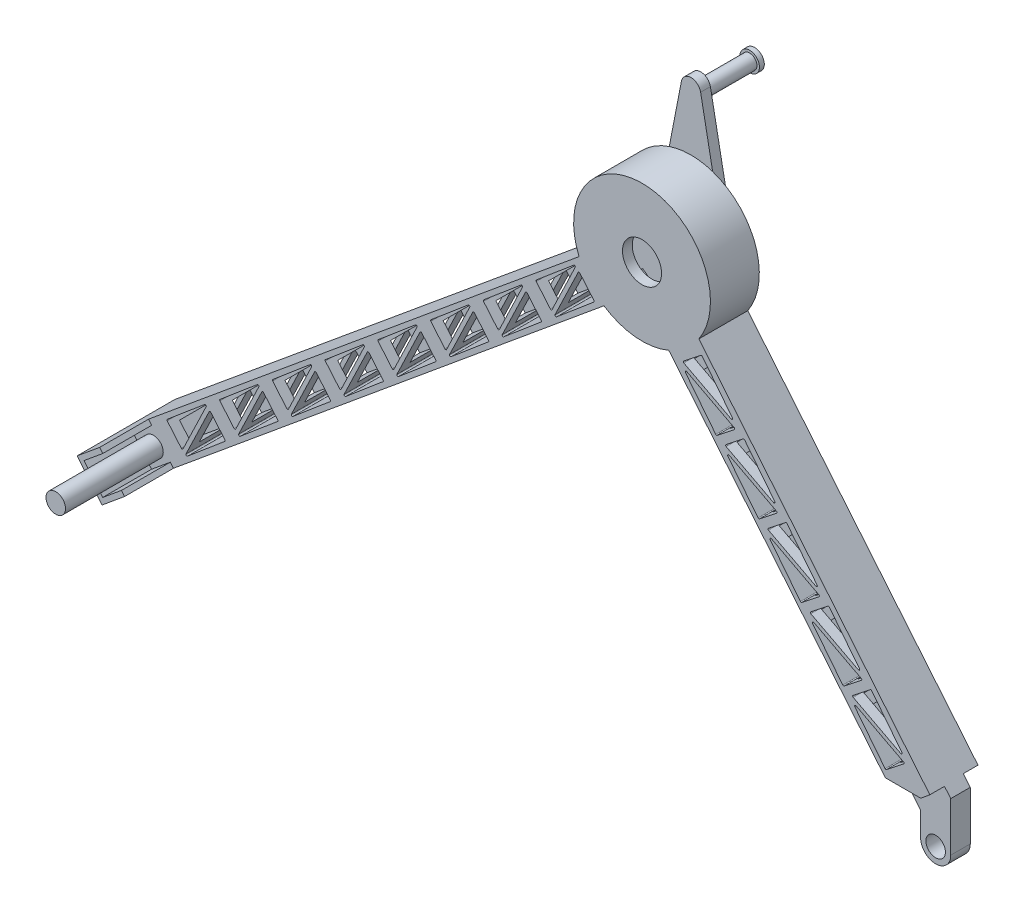
SolidWorks part; units mm, degrees
ref_plane "Front Plane" through (0, 0, 0) normal (0, 0, 1) x (1, 0, 0)
ref_plane "Top Plane" through (0, 0, 0) normal (0, 1, 0) x (1, 0, 0)
ref_plane "Right Plane" through (0, 0, 0) normal (1, 0, 0) x (0, 0, -1)
sketch "Sketch1" plane through (0, 0, 0) normal (0, 0, 1) x (1, 0, 0)
  line L0 (-491.963, 0) -> (712.4353, 0) construction
  line L3 (-479.2178, -15.413) -> (-19.4352, 364.7883)
  line L4 (46.852, 358.5081) -> (289.5642, 64.9929)
  line L5 (-504.7082, 15.413) -> (-44.9257, 395.6142)
  line L6 (77.6779, 383.9986) -> (320.3902, 90.4834)
  line L7 (-504.7082, 15.413) -> (-479.2178, -15.413)
  line L8 (289.5642, 64.9929) -> (320.3902, 90.4834)
  arc A0 (-19.4352, 364.7883) -> (46.852, 358.5081) centre (19.5162, 422.95) ccw
  arc A1 (77.6779, 383.9986) -> (-44.9257, 395.6142) centre (19.5162, 422.95) ccw
  dimension "D4" = 140
  dimension "D1" = 663.7
  dimension "D3" = 422.95
extrude "Boss-Extrude1" add sketch "Sketch1" along normal blind 50
shell "Shell1" thickness 10
sketch "Sketch2" plane through (0, 0, 0) normal (0, 0, 1) x (1, 0, 0)
  line L0 (289.5642, 64.9929) -> (289.5642, 40.3364)
  line L1 (46.852, 358.5081) -> (289.5642, 64.9929) construction
  line L2 (289.5642, 64.9929) -> (320.3902, 90.4834) construction
  line L3 (289.5642, 64.9929) -> (320.3902, 90.4834)
  line L4 (320.3902, 90.4834) -> (320.3902, 40.3364)
  arc A0 (289.5642, 40.3364) -> (320.3902, 40.3364) centre (304.9772, 40.3364) ccw
extrude "Boss-Extrude2" add sketch "Sketch2" along normal blind 50
sketch "Sketch3" plane through (0, 0, 50) normal (0, 0, 1) x (1, 0, 0)
  circle A0 centre (304.9772, 40.3364) radius 10
  dimension "D1" = 20
extrude "Cut-Extrude1" cut sketch "Sketch3" against normal blind 50
sketch "Sketch4" plane through (320.3902, 0, 0) normal (1, 0, 0) x (0, 0, -1)
  line L0 (-50, 24.9234) -> (0, 24.9234) construction
  line L1 (-50, 90.4834) -> (-35, 90.4834)
  line L2 (-50, 90.4834) -> (-50, 24.9234)
  line L3 (-50, 24.9234) -> (-35, 24.9234)
  line L4 (-35, 90.4834) -> (-35, 24.9234)
  line L6 (0, 90.4834) -> (-15, 90.4834)
  line L7 (0, 90.4834) -> (0, 24.9234)
  line L8 (0, 24.9234) -> (-15, 24.9234)
  line L9 (-15, 90.4834) -> (-15, 24.9234)
  dimension "D1" = 20
extrude "Cut-Extrude2" cut sketch "Sketch4" against normal blind 50
sketch "Sketch6" plane through (270.3902, 0, 0) normal (1, 0, 0) x (0, 0, -1)
  line L0 (-50, 88.1804) -> (-35, 88.1804) construction
  line L1 (-50, 90.4834) -> (-35.0332, 90.4834)
  line L2 (-50, 90.4834) -> (-50, 88.1804)
  line L3 (-50, 88.1804) -> (-35.0332, 88.1804)
  line L4 (-35.0332, 90.4834) -> (-35.0332, 88.1804)
  line L5 (0, -15.413) -> (0, 364.7883) construction
  line L6 (-15, 90.4834) -> (0, 90.4834)
  line L7 (-15, 90.4834) -> (-15, 88.1804)
  line L8 (-15, 88.1804) -> (0, 88.1804)
  line L9 (0, 90.4834) -> (0, 88.1804)
  line L10 (0, 88.1804) -> (-15, 88.1804) construction
extrude "Cut-Extrude3" cut sketch "Sketch6" against normal blind 50
sketch "Sketch7" plane through (0, 0, 50) normal (0, 0, 1) x (1, 0, 0)
  line L0 (304.698, 90.4834) -> (314.0176, 98.1898)
  line L1 (320.3902, 90.4834) -> (77.6779, 383.9986) construction
  line L2 (314.0176, 98.1898) -> (320.3902, 90.4834)
  line L3 (320.3902, 90.4834) -> (304.698, 90.4834)
  line L4 (304.698, 90.4834) -> (320.3902, 90.4834) construction
extrude "Cut-Extrude4" cut sketch "Sketch7" against normal up to surface (15 mm away) up to face at (293.083, 73.2709, 35)
sketch "Sketch8" plane through (0, 0, 0) normal (0, 0, -1) x (-1, 0, 0)
  line L0 (-304.698, 90.4834) -> (-313.2874, 99.0728)
  line L1 (-320.3902, 90.4834) -> (-77.6779, 383.9986) construction
  line L2 (-313.2874, 99.0728) -> (-320.3902, 90.4834)
  line L3 (-320.3902, 90.4834) -> (-304.698, 90.4834)
extrude "Cut-Extrude5" cut sketch "Sketch8" against normal up to surface (15 mm away) up to face at (295.6816, 71.4073, 15)
sketch "Sketch9" plane through (0, 0, 0) normal (0, 0, 1) x (1, 0, 0)
  line L0 (-504.7082, 15.413) -> (-479.2178, -15.413)
  line L1 (-479.2178, -15.413) -> (-483.071, -18.5993)
  line L2 (-483.071, -18.5993) -> (-508.5615, 12.2267)
  line L3 (-508.5615, 12.2267) -> (-504.7082, 15.413)
  dimension "D1" = 5
extrude "Boss-Extrude3" add sketch "Sketch9" along normal blind 100
sketch "Sketch10" plane through (0, 0, 50) normal (0, 0, 1) x (1, 0, 0)
  line L0 (-479.2178, -15.413) -> (-459.9516, 0.5186)
  line L1 (-479.2178, -15.413) -> (-19.4352, 364.7883) construction
  line L2 (-459.9516, 0.5186) -> (-463.1379, 4.3718)
  line L3 (-463.1379, 4.3718) -> (-482.4041, -11.5597)
  line L4 (-504.7082, 15.413) -> (-479.2178, -15.413) construction
  line L5 (-482.4041, -11.5597) -> (-479.2178, -15.413)
  line L6 (-504.7082, 15.413) -> (-485.442, 31.3445)
  line L7 (-44.9257, 395.6142) -> (-504.7082, 15.413) construction
  line L8 (-485.442, 31.3445) -> (-482.2557, 27.4912)
  line L9 (-482.2557, 27.4912) -> (-501.5219, 11.5597)
  line L10 (-501.5219, 11.5597) -> (-504.7082, 15.413)
  dimension "D1" = 5
  dimension "D2" = 25
extrude "Boss-Extrude4" add sketch "Sketch10" along normal up to surface (50 mm away) up to face at (-493.8896, -1.5932, 100)
sketch "Sketch11" plane through (0, 0, 50) normal (0, 0, 1) x (1, 0, 0)
  line L0 (-466.2504, 40.8221) -> (-428.047, 73.0788)
  line L1 (-426.5003, 71.8821) -> (-450.2175, 22.4684)
  line L2 (-451.8831, 22.256) -> (-466.3694, 39.4129)
  line L3 (-445.6127, 18.399) -> (-407.4092, 50.6557)
  line L4 (-407.2903, 52.0649) -> (-421.7766, 69.2218)
  line L5 (-423.4422, 69.0094) -> (-447.1594, 19.5958)
  line L9 (-44.9257, 395.6142) -> (-485.442, 31.3445) construction
  line L10 (-44.9257, 395.6142) -> (-485.442, 31.3445)
  line L11 (-470.773, 43.4745) -> (-429.0952, 77.9385)
  line L14 (-397.9377, 66.8642) -> (-412.424, 84.0212)
  line L15 (-412.3051, 85.4304) -> (-374.1016, 117.6871)
  line L16 (-372.5549, 116.4903) -> (-396.2721, 67.0767)
  line L17 (-369.4968, 113.6177) -> (-393.214, 64.204)
  line L18 (-391.6673, 63.0072) -> (-353.4639, 95.2639)
  line L19 (-353.3449, 96.6731) -> (-367.8312, 113.8301)
  line L20 (-343.9923, 111.4725) -> (-358.4786, 128.6294)
  line L21 (-358.3597, 130.0386) -> (-320.1562, 162.2954)
  line L22 (-318.6095, 161.0986) -> (-342.3267, 111.6849)
  line L23 (-315.5514, 158.2259) -> (-339.2686, 108.8123)
  line L24 (-337.722, 107.6155) -> (-299.5185, 139.8722)
  line L25 (-299.3996, 141.2814) -> (-313.8858, 158.4383)
  line L26 (-290.047, 156.0808) -> (-304.5332, 173.2377)
  line L27 (-304.4143, 174.6469) -> (-266.2108, 206.9036)
  line L28 (-264.6642, 205.7068) -> (-288.3813, 156.2932)
  line L29 (-261.6061, 202.8342) -> (-285.3233, 153.4205)
  line L30 (-283.7766, 152.2237) -> (-245.5731, 184.4805)
  line L31 (-245.4542, 185.8897) -> (-259.9405, 203.0466)
  line L32 (-236.1016, 200.689) -> (-250.5879, 217.846)
  line L33 (-250.4689, 219.2552) -> (-212.2655, 251.5119)
  line L34 (-210.7188, 250.3151) -> (-234.436, 200.9014)
  line L35 (-207.6607, 247.4424) -> (-231.3779, 198.0288)
  line L36 (-229.8312, 196.832) -> (-191.6277, 229.0887)
  line L37 (-191.5088, 230.4979) -> (-205.9951, 247.6549)
  line L38 (-182.1562, 245.2973) -> (-196.6425, 262.4542)
  line L39 (-196.5236, 263.8634) -> (-158.3201, 296.1201)
  line L40 (-156.7734, 294.9233) -> (-180.4906, 245.5097)
  line L41 (-153.7153, 292.0507) -> (-177.4325, 242.637)
  line L42 (-175.8858, 241.4403) -> (-137.6824, 273.697)
  line L43 (-137.5634, 275.1062) -> (-152.0497, 292.2631)
  line L44 (-128.2108, 289.9055) -> (-142.6971, 307.0625)
  line L45 (-142.5782, 308.4717) -> (-104.3747, 340.7284)
  line L46 (-102.828, 339.5316) -> (-126.5452, 290.118)
  line L47 (-99.7699, 336.6589) -> (-123.4871, 287.2453)
  line L48 (-121.9405, 286.0485) -> (-83.737, 318.3052)
  line L49 (-83.6181, 319.7144) -> (-98.1043, 336.8714)
  line L50 (-74.2655, 334.5138) -> (-88.7517, 351.6707)
  line L51 (-88.6328, 353.0799) -> (-50.4293, 385.3366)
  line L52 (-48.8827, 384.1399) -> (-72.5999, 334.7262)
  line L53 (-45.8246, 381.2672) -> (-69.5418, 331.8536)
  line L54 (-67.9951, 330.6568) -> (-29.7916, 362.9135)
  line L55 (-29.6727, 364.3227) -> (-44.159, 381.4796)
  arc A0 (-445.6127, 18.399) -> (-447.1594, 19.5958) centre (-446.2578, 19.163) cw
  arc A1 (-407.4092, 50.6557) -> (-407.2903, 52.0649) centre (-408.0544, 51.4197) ccw
  arc A2 (-421.7766, 69.2218) -> (-423.4422, 69.0094) centre (-422.5407, 68.5767) ccw
  arc A3 (-450.2175, 22.4684) -> (-451.8831, 22.256) centre (-451.119, 22.9011) cw
  arc A4 (-466.3694, 39.4129) -> (-466.2504, 40.8221) centre (-465.6053, 40.0581) cw
  arc A5 (-426.5003, 71.8821) -> (-428.047, 73.0788) centre (-427.4018, 72.3148) ccw
  arc A6 (-412.424, 84.0212) -> (-412.3051, 85.4304) centre (-411.6599, 84.6663) cw
  arc A7 (-396.2721, 67.0767) -> (-397.9377, 66.8642) centre (-397.1736, 67.5094) cw
  arc A8 (-372.5549, 116.4903) -> (-374.1016, 117.6871) centre (-373.4564, 116.923) ccw
  arc A9 (-367.8312, 113.8301) -> (-369.4968, 113.6177) centre (-368.5953, 113.1849) ccw
  arc A10 (-391.6673, 63.0072) -> (-393.214, 64.204) centre (-392.3125, 63.7713) cw
  arc A11 (-353.4639, 95.2639) -> (-353.3449, 96.6731) centre (-354.109, 96.028) ccw
  arc A12 (-358.4786, 128.6294) -> (-358.3597, 130.0386) centre (-357.7145, 129.2746) cw
  arc A13 (-342.3267, 111.6849) -> (-343.9923, 111.4725) centre (-343.2283, 112.1176) cw
  arc A14 (-318.6095, 161.0986) -> (-320.1562, 162.2954) centre (-319.5111, 161.5313) ccw
  arc A15 (-313.8858, 158.4383) -> (-315.5514, 158.2259) centre (-314.6499, 157.7932) ccw
  arc A16 (-337.722, 107.6155) -> (-339.2686, 108.8123) centre (-338.3671, 108.3796) cw
  arc A17 (-299.5185, 139.8722) -> (-299.3996, 141.2814) centre (-300.1636, 140.6363) ccw
  arc A18 (-304.5332, 173.2377) -> (-304.4143, 174.6469) centre (-303.7692, 173.8828) cw
  arc A19 (-288.3813, 156.2932) -> (-290.047, 156.0808) centre (-289.2829, 156.7259) cw
  arc A20 (-264.6642, 205.7068) -> (-266.2108, 206.9036) centre (-265.5657, 206.1395) ccw
  arc A21 (-259.9405, 203.0466) -> (-261.6061, 202.8342) centre (-260.7045, 202.4015) ccw
  arc A22 (-283.7766, 152.2237) -> (-285.3233, 153.4205) centre (-284.4217, 152.9878) cw
  arc A23 (-245.5731, 184.4805) -> (-245.4542, 185.8897) centre (-246.2183, 185.2445) ccw
  arc A24 (-250.5879, 217.846) -> (-250.4689, 219.2552) centre (-249.8238, 218.4911) cw
  arc A25 (-234.436, 200.9014) -> (-236.1016, 200.689) centre (-235.3375, 201.3341) cw
  arc A26 (-210.7188, 250.3151) -> (-212.2655, 251.5119) centre (-211.6203, 250.7478) ccw
  arc A27 (-205.9951, 247.6549) -> (-207.6607, 247.4424) centre (-206.7592, 247.0097) ccw
  arc A28 (-229.8312, 196.832) -> (-231.3779, 198.0288) centre (-230.4763, 197.5961) cw
  arc A29 (-191.6277, 229.0887) -> (-191.5088, 230.4979) centre (-192.2729, 229.8528) ccw
  arc A30 (-196.6425, 262.4542) -> (-196.5236, 263.8634) centre (-195.8784, 263.0993) cw
  arc A31 (-180.4906, 245.5097) -> (-182.1562, 245.2973) centre (-181.3921, 245.9424) cw
  arc A32 (-156.7734, 294.9233) -> (-158.3201, 296.1201) centre (-157.6749, 295.3561) ccw
  arc A33 (-152.0497, 292.2631) -> (-153.7153, 292.0507) centre (-152.8138, 291.618) ccw
  arc A34 (-175.8858, 241.4403) -> (-177.4325, 242.637) centre (-176.531, 242.2043) cw
  arc A35 (-137.6824, 273.697) -> (-137.5634, 275.1062) centre (-138.3275, 274.461) ccw
  arc A36 (-142.6971, 307.0625) -> (-142.5782, 308.4717) centre (-141.933, 307.7076) cw
  arc A37 (-126.5452, 290.118) -> (-128.2108, 289.9055) centre (-127.4468, 290.5507) cw
  arc A38 (-102.828, 339.5316) -> (-104.3747, 340.7284) centre (-103.7296, 339.9643) ccw
  arc A39 (-98.1043, 336.8714) -> (-99.7699, 336.6589) centre (-98.8684, 336.2262) ccw
  arc A40 (-121.9405, 286.0485) -> (-123.4871, 287.2453) centre (-122.5856, 286.8126) cw
  arc A41 (-83.737, 318.3052) -> (-83.6181, 319.7144) centre (-84.3821, 319.0693) ccw
  arc A42 (-88.7517, 351.6707) -> (-88.6328, 353.0799) centre (-87.9877, 352.3159) cw
  arc A43 (-72.5999, 334.7262) -> (-74.2655, 334.5138) centre (-73.5014, 335.1589) cw
  arc A44 (-48.8827, 384.1399) -> (-50.4293, 385.3366) centre (-49.7842, 384.5726) ccw
  arc A45 (-44.159, 381.4796) -> (-45.8246, 381.2672) centre (-44.923, 380.8345) ccw
  arc A46 (-67.9951, 330.6568) -> (-69.5418, 331.8536) centre (-68.6402, 331.4208) cw
  arc A47 (-29.7916, 362.9135) -> (-29.6727, 364.3227) centre (-30.4368, 363.6775) ccw
  point P21 (-450.8861, 21.0753)
  point P24 (-467.0145, 40.177)
  point P27 (-424.4805, 76.0901)
  dimension "D5" = 1
  dimension "D1" = 50
  dimension "D2" = 25
  dimension "D3" = 4
  dimension "D4" = 5
  dimension "D6" = 8
extrude "Cut-Extrude6" cut sketch "Sketch11" against normal blind 100 contours L1 A5 L0 A4 L2 A3 | L4 A2 L5 A0 L3 A1 | L16 A8 L15 A6 L14 A7 | L18 A11 L19 A9 L17 A10 | L22 A14 L21 A12 L20 A13 | L24 A17 L25 A15 L23 A16 | L28 A20 L27 A18 L26 A19 | L30 A23 L31 A21 L29 A22 | L34 A26 L33 A24 L32 A25 | L36 A29 L37 A27 L35 A28 | L40 A32 L39 A30 L38 A31 | L42 A35 L43 A33 L41 A34 | L46 A38 L45 A36 L44 A37 | L48 A41 L49 A39 L47 A40 | L54 A47 L55 A45 L53 A46 | L52 A43 L50 A42 L51 A44
sketch "Sketch12" plane through (0, 0, 50) normal (0, 0, 1) x (1, 0, 0)
  line L0 (269.659, 98.2793) -> (287.2936, 112.1801)
  line L1 (287.1374, 113.8519) -> (238.5497, 139.2183)
  line L2 (237.3016, 137.7128) -> (268.2546, 98.4456)
  line L3 (254.4529, 160.6925) -> (285.4059, 121.4254)
  line L4 (284.1577, 119.9198) -> (235.5701, 145.2862)
  line L5 (235.4138, 146.958) -> (253.0485, 160.8588)
  line L6 (192.0801, 199.3621) -> (209.7147, 213.2629)
  line L7 (211.1191, 213.0966) -> (242.0721, 173.8294)
  line L8 (240.824, 172.3239) -> (192.2363, 197.6903)
  line L9 (193.9678, 190.1169) -> (224.9208, 150.8497)
  line L10 (226.3252, 150.6834) -> (243.9599, 164.5842)
  line L11 (243.8036, 166.256) -> (195.216, 191.6224)
  line L12 (148.7464, 251.7662) -> (166.381, 265.667)
  line L13 (167.7854, 265.5007) -> (198.7384, 226.2335)
  line L14 (197.4903, 224.728) -> (148.9026, 250.0944)
  line L15 (150.6341, 242.521) -> (181.5871, 203.2538)
  line L16 (182.9915, 203.0875) -> (200.6261, 216.9883)
  line L17 (200.4699, 218.6601) -> (151.8822, 244.0265)
  line L18 (105.4126, 304.1703) -> (123.0473, 318.0711)
  line L19 (124.4517, 317.9048) -> (155.4047, 278.6376)
  line L20 (154.1565, 277.1321) -> (105.5689, 302.4985)
  line L21 (107.3004, 294.925) -> (138.2533, 255.6578)
  line L22 (139.6578, 255.4916) -> (157.2924, 269.3924)
  line L23 (157.1361, 271.0642) -> (108.5485, 296.4306)
  line L24 (62.0789, 356.5743) -> (79.7135, 370.4751)
  line L25 (81.1179, 370.3089) -> (112.0709, 331.0417)
  line L26 (110.8228, 329.5361) -> (62.2351, 354.9025)
  line L27 (63.9666, 347.3291) -> (94.9196, 308.0619)
  line L28 (96.324, 307.8956) -> (113.9587, 321.7964)
  line L29 (113.8024, 323.4682) -> (65.2148, 348.8346)
  arc A0 (285.4059, 121.4254) -> (284.1577, 119.9198) centre (284.6205, 120.8063) cw
  arc A1 (235.5701, 145.2862) -> (235.4138, 146.958) centre (236.0329, 146.1727) cw
  arc A2 (253.0485, 160.8588) -> (254.4529, 160.6925) centre (253.6675, 160.0735) cw
  arc A3 (269.659, 98.2793) -> (268.2546, 98.4456) centre (269.0399, 99.0647) cw
  arc A4 (287.2936, 112.1801) -> (287.1374, 113.8519) centre (286.6746, 112.9655) ccw
  arc A5 (237.3016, 137.7128) -> (238.5497, 139.2183) centre (238.0869, 138.3319) cw
  arc A6 (209.7147, 213.2629) -> (211.1191, 213.0966) centre (210.3338, 212.4776) cw
  arc A7 (192.2363, 197.6903) -> (192.0801, 199.3621) centre (192.6991, 198.5768) cw
  arc A8 (242.0721, 173.8294) -> (240.824, 172.3239) centre (241.2868, 173.2104) cw
  arc A9 (193.9678, 190.1169) -> (195.216, 191.6224) centre (194.7532, 190.7359) cw
  arc A10 (226.3252, 150.6834) -> (224.9208, 150.8497) centre (225.7062, 151.4687) cw
  arc A11 (243.9599, 164.5842) -> (243.8036, 166.256) centre (243.3408, 165.3695) ccw
  arc A12 (166.381, 265.667) -> (167.7854, 265.5007) centre (167.0001, 264.8816) cw
  arc A13 (148.9026, 250.0944) -> (148.7464, 251.7662) centre (149.3654, 250.9808) cw
  arc A14 (198.7384, 226.2335) -> (197.4903, 224.728) centre (197.9531, 225.6145) cw
  arc A15 (150.6341, 242.521) -> (151.8822, 244.0265) centre (151.4194, 243.14) cw
  arc A16 (182.9915, 203.0875) -> (181.5871, 203.2538) centre (182.3724, 203.8728) cw
  arc A17 (200.6261, 216.9883) -> (200.4699, 218.6601) centre (200.0071, 217.7736) ccw
  arc A18 (123.0473, 318.0711) -> (124.4517, 317.9048) centre (123.6663, 317.2857) cw
  arc A19 (105.5689, 302.4985) -> (105.4126, 304.1703) centre (106.0317, 303.3849) cw
  arc A20 (155.4047, 278.6376) -> (154.1565, 277.1321) centre (154.6193, 278.0185) cw
  arc A21 (107.3004, 294.925) -> (108.5485, 296.4306) centre (108.0857, 295.5441) cw
  arc A22 (139.6578, 255.4916) -> (138.2533, 255.6578) centre (139.0387, 256.2769) cw
  arc A23 (157.2924, 269.3924) -> (157.1361, 271.0642) centre (156.6733, 270.1777) ccw
  arc A24 (79.7135, 370.4751) -> (81.1179, 370.3089) centre (80.3326, 369.6898) cw
  arc A25 (62.2351, 354.9025) -> (62.0789, 356.5743) centre (62.6979, 355.789) cw
  arc A26 (112.0709, 331.0417) -> (110.8228, 329.5361) centre (111.2856, 330.4226) cw
  arc A27 (63.9666, 347.3291) -> (65.2148, 348.8346) centre (64.752, 347.9482) cw
  arc A28 (96.324, 307.8956) -> (94.9196, 308.0619) centre (95.705, 308.681) cw
  arc A29 (113.9587, 321.7964) -> (113.8024, 323.4682) centre (113.3396, 322.5818) ccw
  point P16 (268.8736, 97.6603)
  point P19 (288.5072, 113.1368)
  point P22 (234.412, 141.3785)
  dimension "D4" = 1
  dimension "D1" = 50
  dimension "D2" = 25
  dimension "D3" = 4
  dimension "D5" = 5
extrude "Cut-Extrude7" cut sketch "Sketch12" against normal blind 100
sketch "Sketch13" plane through (0, 0, 50) normal (0, 0, 1) x (1, 0, 0)
  line L0 (-501.5219, 11.5597) -> (-482.2557, 27.4912) construction
  line L1 (-482.4041, -11.5597) -> (-501.5219, 11.5597) construction
  circle A0 centre (-480.4033, 9.5589) radius 10
  dimension "D2" = 20
  dimension "D1" = 15
  dimension "D3" = 15
extrude "Boss-Extrude5" add sketch "Sketch13" along normal blind 100
sketch "Sketch15" plane through (0, 0, 0) normal (0, 0, -1) x (-1, 0, 0)
  circle A0 centre (-19.5162, 422.95) radius 20
  dimension "D1" = 40
extrude "Cut-Extrude8" cut sketch "Sketch15" against normal blind 100
sketch "Sketch16" plane through (0, 0, 0) normal (0, 0, -1) x (-1, 0, 0)
  line L0 (-29.4633, 553.4567) -> (-52.0283, 435.9101)
  line L1 (-9.8254, 553.475) -> (12.9473, 436.0314)
  arc A1 (-9.8254, 553.475) -> (-29.4633, 553.4567) centre (-19.6426, 551.5715) ccw
  arc A2 (-52.0283, 435.9101) -> (12.9473, 436.0314) centre (-19.5162, 422.95) ccw
  dimension "D3" = 10
extrude "Boss-Extrude6" add sketch "Sketch16" along normal blind 10
sketch "Sketch17" plane through (0, 0, -10) normal (0, 0, -1) x (-1, 0, 0)
  line L0 (-30.9322, 545.8049) -> (-8.3382, 545.8049) construction
  line L1 (-29.4633, 553.4567) -> (-52.0283, 435.9101) construction
  line L2 (12.9473, 436.0314) -> (-9.8254, 553.475) construction
  circle A0 centre (-19.6352, 545.8049) radius 7.5
  point P8 (0, 0)
  point P9 (-19.6352, 545.8049)
  dimension "D1" = 15
extrude "Boss-Extrude7" add sketch "Sketch17" along normal blind 50
sketch "Sketch18" plane through (0, 0, -60) normal (0, 0, -1) x (-1, 0, 0)
  circle A0 centre (-19.6352, 545.8049) radius 10
  dimension "D1" = 20
extrude "Boss-Extrude8" add sketch "Sketch18" along normal blind 5
sketch "Sketch19" plane through (0, 0, 0) normal (0, 0, 1) x (1, 0, 0)
  circle A0 centre (19.5162, 422.95) radius 20
extrude "Cut-Extrude10" cut sketch "Sketch19" against normal blind 47
